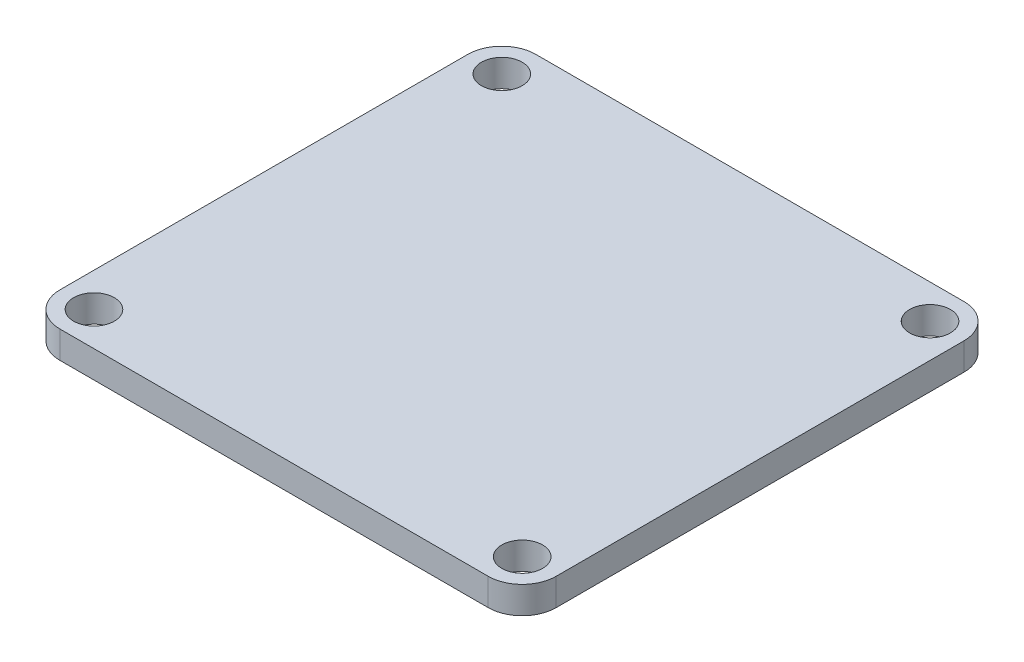
SolidWorks part; units mm, degrees
ref_plane "Front" through (0, 0, 0) normal (0, 0, 1) x (1, 0, 0)
ref_plane "Top" through (0, 0, 0) normal (0, 1, 0) x (1, 0, 0)
ref_plane "Right" through (0, 0, 0) normal (1, 0, 0) x (0, 0, -1)
sketch "Sketch2" plane through (0, 0, 0) normal (0, 1, 0) x (1, 0, 0)
  line L0 (-31.5, 35) -> (-31.5, -35) construction
  line L1 (-31.5, -35) -> (31.5, -35)
  line L2 (-36.5, -30) -> (-36.5, 30)
  line L3 (-31.5, 35) -> (31.5, 35)
  line L4 (36.5, -30) -> (36.5, 30)
  line L5 (-36.5, -35) -> (36.5, 35) construction
  line L6 (-36.5, 35) -> (36.5, -35) construction
  line L7 (-36.5, -30) -> (36.5, -30) construction
  line L8 (31.5, -35) -> (31.5, 35) construction
  line L9 (36.5, 30) -> (-36.5, 30) construction
  arc A0 (-31.5, -35) -> (-36.5, -30) centre (-31.5, -30) cw
  arc A1 (31.5, -35) -> (36.5, -30) centre (31.5, -30) ccw
  arc A2 (31.5, 35) -> (36.5, 30) centre (31.5, 30) cw
  arc A3 (-36.5, 30) -> (-31.5, 35) centre (-31.5, 30) cw
  circle A4 centre (-31.5, 30) radius 3
  circle A5 centre (-31.5, -30) radius 3
  circle A6 centre (31.5, 30) radius 3
  circle A7 centre (31.5, -30) radius 3
  point P0 (0, 0)
  dimension "D3" = 5
  dimension "D1" = 73
  dimension "D2" = 70
extrude "Boss-Extrude1" add sketch "Sketch2" along normal blind 4
